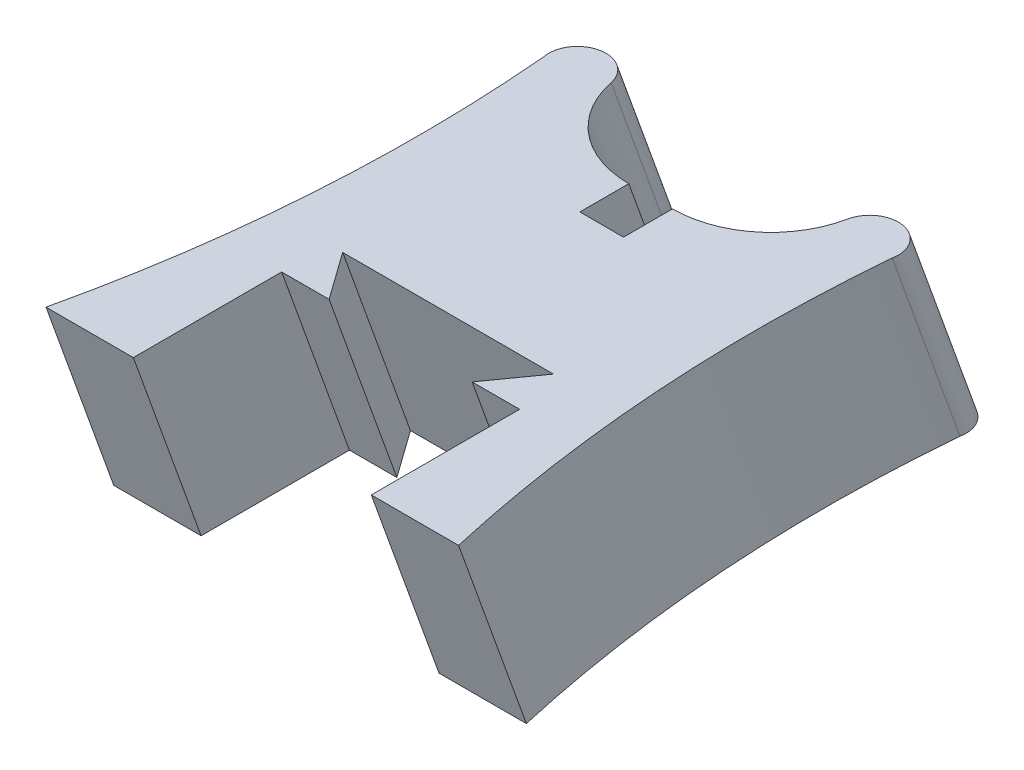
SolidWorks part; units mm, degrees
ref_plane "Front Plane" through (0, 0, 0) normal (0, 0, 1) x (1, 0, 0)
ref_plane "Top Plane" through (0, 0, 0) normal (0, 1, 0) x (1, 0, 0)
ref_plane "Right Plane" through (0, 0, 0) normal (1, 0, 0) x (0, 0, -1)
sketch "Sketch2" plane through (0, 0, 0) normal (0, 1, 0) x (1, 0, 0)
  line L0 (6.9596, -10.3777) -> (4.0132, -10.3777)
  line L1 (4.0132, -10.3777) -> (4.0132, -5.3739)
  line L2 (4.0132, -5.3739) -> (2.413, -5.3739)
  line L3 (2.413, -5.3739) -> (3.556, -3.7737)
  line L4 (3.556, -3.7737) -> (-3.556, -3.7737)
  line L5 (-3.556, -3.7737) -> (-2.413, -5.3739)
  line L6 (-2.413, -5.3739) -> (-4.0132, -5.3739)
  line L7 (-4.0132, -5.3739) -> (-4.0132, -10.3777)
  line L8 (-4.0132, -10.3777) -> (-6.9596, -10.3777)
  line L9 (0, 0) -> (0, -50000) construction
  line L10 (-0.7366, 3.0589) -> (-0.7366, 1.4079)
  line L11 (-0.7366, 1.4079) -> (0.7366, 1.4079)
  line L12 (0.7366, 1.4079) -> (0.7366, 3.0589)
  line L13 (0, 0) -> (50000, 0) construction
  arc A0 (3.9869, 5.7131) -> (5.8777, 5.3274) centre (4.9323, 5.5202) cw
  arc A1 (0.7366, 3.0589) -> (3.9869, 5.7131) centre (0.7366, 6.3761) ccw
  arc A2 (5.8777, 5.3274) -> (6.9596, -10.3777) centre (56.4865, 0.9238) ccw
  arc A3 (-0.7366, 3.0589) -> (-3.9869, 5.7131) centre (-0.7366, 6.3761) cw
  arc A4 (-3.9869, 5.7131) -> (-5.8777, 5.3274) centre (-4.9323, 5.5202) ccw
  arc A5 (-5.8777, 5.3274) -> (-6.9596, -10.3777) centre (-56.4865, 0.9238) cw
  dimension "D10" = 0.9649
  dimension "D13" = 50.8
  dimension "D1" = 7.112
  dimension "D2" = 1.6002
  dimension "D3" = 1.6002
  dimension "D4" = 4.826
  dimension "D5" = 5.0038
  dimension "D6" = 2.9464
  dimension "D7" = 5.1816
  dimension "D8" = 1.4732
  dimension "D9" = 1.651
sketch "Sketch4" plane through (0, 0, 0) normal (1, 0, 0) x (0, 0, -1)
  line L0 (0, 0) -> (-2.286, 6.35)
  dimension "D1" = 2.286
  dimension "D2" = 6.35
sweep "Sweep1" add profiles "Sketch2" path "Sketch4"
